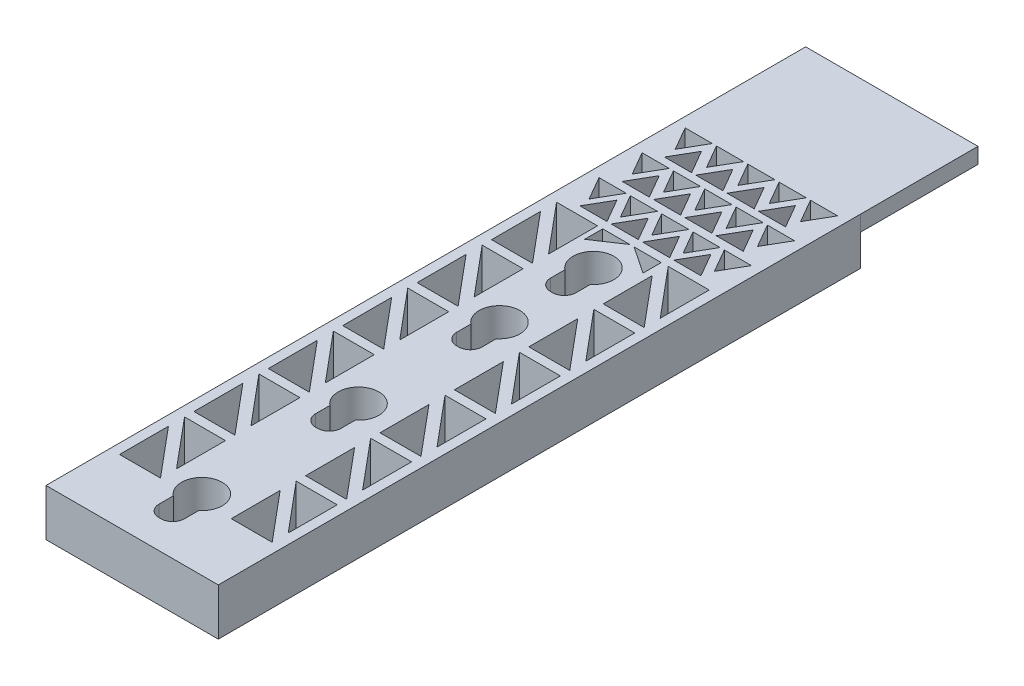
SolidWorks part; units mm, degrees
ref_plane "Front Plane" through (0, 0, 0) normal (0, 0, 1) x (1, 0, 0)
ref_plane "Top Plane" through (0, 0, 0) normal (0, 1, 0) x (1, 0, 0)
ref_plane "Right Plane" through (0, 0, 0) normal (1, 0, 0) x (0, 0, -1)
sketch "Sketch23" plane through (0, 0, 0) normal (0, 1, 0) x (1, 0, 0)
  line L1 (181.0964, 0) -> (203.0964, 0)
  line L2 (181.0964, 0) -> (181.0964, -82)
  line L3 (181.0964, -82) -> (203.0964, -82)
  line L4 (203.0964, 0) -> (203.0964, -82)
  circle A0 centre (192, -73) radius 2.6
  circle A1 centre (192, -53) radius 2.6
  circle A2 centre (192, -35) radius 2.6
  circle A3 centre (192, -23) radius 2.6
  dimension "D9" = 5.2
  dimension "D10" = 5.2
  dimension "D11" = 5.2
  dimension "D12" = 5.2
  dimension "D2" = 23
  dimension "D3" = 20
  dimension "D4" = 18
  dimension "D5" = 12
  dimension "D6" = 22
  dimension "D7" = 82
extrude "Boss-Extrude3" add sketch "Sketch23" against normal blind 6
sketch "Sketch25" plane through (0, 0, 0) normal (0, 1, 0) x (1, 0, 0)
  line L7 (190.375, -78.35) -> (193.625, -78.35)
  line L8 (190.375, -78.35) -> (190.375, -72.85)
  line L9 (190.375, -72.85) -> (193.625, -72.85)
  line L10 (193.625, -78.35) -> (193.625, -72.85)
  line L11 (190.375, -78.35) -> (193.625, -72.85) construction
  line L12 (190.375, -72.85) -> (193.625, -78.35) construction
  line L13 (190.375, -58.35) -> (193.625, -58.35)
  line L14 (190.375, -58.35) -> (190.375, -52.85)
  line L15 (190.375, -52.85) -> (193.625, -52.85)
  line L16 (193.625, -58.35) -> (193.625, -52.85)
  line L17 (190.375, -58.35) -> (193.625, -52.85) construction
  line L18 (190.375, -52.85) -> (193.625, -58.35) construction
  line L19 (190.375, -40.35) -> (193.625, -40.35)
  line L20 (190.375, -40.35) -> (190.375, -34.85)
  line L21 (190.375, -34.85) -> (193.625, -34.85)
  line L22 (193.625, -40.35) -> (193.625, -34.85)
  line L23 (190.375, -40.35) -> (193.625, -34.85) construction
  line L24 (190.375, -34.85) -> (193.625, -40.35) construction
  line L25 (190.375, -28.35) -> (193.625, -28.35)
  line L26 (190.375, -28.35) -> (190.375, -22.85)
  line L27 (190.375, -22.85) -> (193.625, -22.85)
  line L28 (193.625, -28.35) -> (193.625, -22.85)
  line L29 (190.375, -28.35) -> (193.625, -22.85) construction
  line L30 (190.375, -22.85) -> (193.625, -28.35) construction
  circle A1 centre (192, -73) radius 2.6 construction
  circle A2 centre (192, -53) radius 2.6 construction
  circle A3 centre (192, -35) radius 2.6 construction
  circle A4 centre (192, -23) radius 2.6 construction
  point P7 (192, -75.6)
  point P14 (192, -55.6)
  point P22 (192, -37.6)
  point P29 (192, -25.6)
extrude "Cut-Extrude1" cut sketch "Sketch25" against normal blind 15.322
fillet "Fillet1" radius 1.5 6 edges at (193.625, -3, 78.35) (190.375, -3, 78.35) (193.625, -3, 40.35) (190.375, -3, 40.35) (190.375, -3, 28.35) (193.625, -3, 28.35)
fillet "Fillet2" radius 1.5 2 edges at (190.375, -3, 58.35) (193.625, -3, 58.35)
sketch "Sketch30" plane through (0, 0, 0) normal (0, 1, 0) x (1, 0, 0)
  line L1 (192.0964, -4.6548) -> (193.8285, -1.6548)
  line L2 (193.8285, -1.6548) -> (190.3644, -1.6548)
  line L3 (190.3644, -1.6548) -> (192.0964, -4.6548)
  circle A0 centre (192.0964, -2.6548) radius 1 construction
  dimension "D1" = 11
extrude "Cut-Extrude7" cut sketch "Sketch30" against normal blind 13.7948
pattern_linear "LPattern3" count 3 spacing 4 along (-1, 0, 0) count 3 spacing 4 along (1, 0, 0) of "Cut-Extrude7"
pattern_linear "LPattern4" count 3 spacing 5.5 along (0, 0, 1) of "LPattern3", "Cut-Extrude7"
sketch "Sketch31" plane through (0, 0, 0) normal (0, 1, 0) x (1, 0, 0)
  line L1 (185.9964, -3.2) -> (184.2644, -6.2)
  line L2 (184.2644, -6.2) -> (187.7285, -6.2)
  line L3 (187.7285, -6.2) -> (185.9964, -3.2)
  circle A0 centre (185.9964, -5.2) radius 1 construction
  dimension "D1" = 4.9
  dimension "D2" = 5.2
extrude "Cut-Extrude8" cut sketch "Sketch31" against normal blind 13.4849
pattern_linear "LPattern5" count 4 spacing 4 along (1, 0, 0) count 3 spacing 5.4 along (0, 0, 1) of "Cut-Extrude8"
sketch "Sketch33" plane through (0, 0, 0) normal (0, 1, 0) x (1, 0, 0)
  line L0 (201.8264, -18.05) -> (196.5964, -18.05)
  line L1 (196.5964, -18.05) -> (201.8264, -24.3028)
  line L2 (201.8264, -24.3028) -> (201.8264, -18.05)
  dimension "D1" = 1.27
  dimension "D2" = 1.05
  dimension "D3" = 6.5
extrude "Cut-Extrude9" cut sketch "Sketch33" against normal blind 53.6723
pattern_linear "LPattern7" count 6 spacing 9.5 along (0, 0, 1) of "Cut-Extrude9"
sketch "Sketch38" plane through (0, 0, 0) normal (0, 1, 0) x (1, 0, 0)
  line L0 (187.5964, -18.08) -> (182.3664, -18.08)
  line L1 (182.3664, -18.08) -> (187.5964, -24.3328)
  line L2 (187.5964, -24.3328) -> (187.5964, -18.08)
  dimension "D1" = 1.27
  dimension "D2" = 1.08
extrude "Cut-Extrude10" cut sketch "Sketch38" against normal blind 24.8037
pattern_linear "LPattern8" count 6 spacing 9.5 along (0, 0, 1) of "Cut-Extrude10"
sketch "Sketch39" plane through (0, 0, 0) normal (0, 1, 0) x (1, 0, 0)
  line L0 (201.8264, -26.35) -> (196.5964, -20.1)
  line L1 (196.5964, -20.1) -> (196.5964, -26.35)
  line L2 (196.5964, -26.35) -> (201.8264, -26.35)
  dimension "D1" = 1.27
  dimension "D2" = 5.23
  dimension "D3" = 1.2
  dimension "D4" = 2.05
extrude "Cut-Extrude11" cut sketch "Sketch39" against normal blind 27.4066
pattern_linear "LPattern9" count 6 spacing 9.5 along (0, 0, 1) of "Cut-Extrude11"
sketch "Sketch40" plane through (0, 0, 0) normal (0, 1, 0) x (1, 0, 0)
  line L0 (187.5964, -26.38) -> (182.3664, -20.13)
  line L1 (182.3664, -20.13) -> (182.3664, -26.38)
  line L2 (182.3664, -26.38) -> (187.5964, -26.38)
  dimension "D1" = 1.27
  dimension "D2" = 2.05
extrude "Cut-Extrude12" cut sketch "Sketch40" against normal blind 18.7522
pattern_linear "LPattern10" count 6 spacing 9.5 along (0, 0, 1) of "Cut-Extrude12"
sketch "Sketch41" plane through (0, 0, 0) normal (0, 1, 0) x (1, 0, 0)
  line L0 (188.2644, -18.08) -> (191.7285, -18.08)
  line L1 (191.7285, -18.08) -> (188.2644, -20.4)
  line L2 (188.2644, -20.4) -> (188.2644, -18.08)
  line L3 (195.7285, -18.08) -> (192.2644, -18.08)
  line L4 (192.2644, -18.08) -> (195.7285, -20.4)
  line L5 (195.7285, -20.4) -> (195.7285, -18.08)
extrude "Cut-Extrude13" cut sketch "Sketch41" against normal blind 6
sketch "Sketch42" plane through (0, 0, 0) normal (0, 1, 0) x (1, 0, 0)
  line L1 (181.0964, 0) -> (203.1, 0)
  line L2 (181.0964, 0) -> (181.0964, 15)
  line L3 (181.0964, 15) -> (203.1, 15)
  line L4 (203.1, 0) -> (203.1, 15)
extrude "Boss-Extrude4" add sketch "Sketch42" against normal blind 2
sketch "Sketch48" plane through (0, -2, 0) normal (0, -1, 0) x (1, 0, 0)
  line L0 (181.0964, -15) -> (181.0964, 0) construction
  line L1 (186.0964, -4) -> (198.1, -4)
  line L2 (186.0964, -4) -> (186.0964, -8)
  line L3 (186.0964, -8) -> (189.0964, -8)
  line L4 (198.1, -4) -> (198.1, -8)
  line L5 (203.1, 0) -> (203.1, -15) construction
  line L6 (181.0964, 0) -> (203.0964, 0) construction
  line L7 (195.1, -8) -> (198.1, -8)
  line L9 (189.0964, -8) -> (189.0964, -12)
  line L10 (189.0964, -12) -> (195.1, -12)
  line L11 (195.1, -8) -> (195.1, -12)
  dimension "D1" = 5
  dimension "D2" = 5
  dimension "D3" = 4
  dimension "D4" = 4
  dimension "D5" = 3
  dimension "D6" = 3
  dimension "D7" = 4
extrude "Boss-Extrude5" add sketch "Sketch48" along normal blind 4
